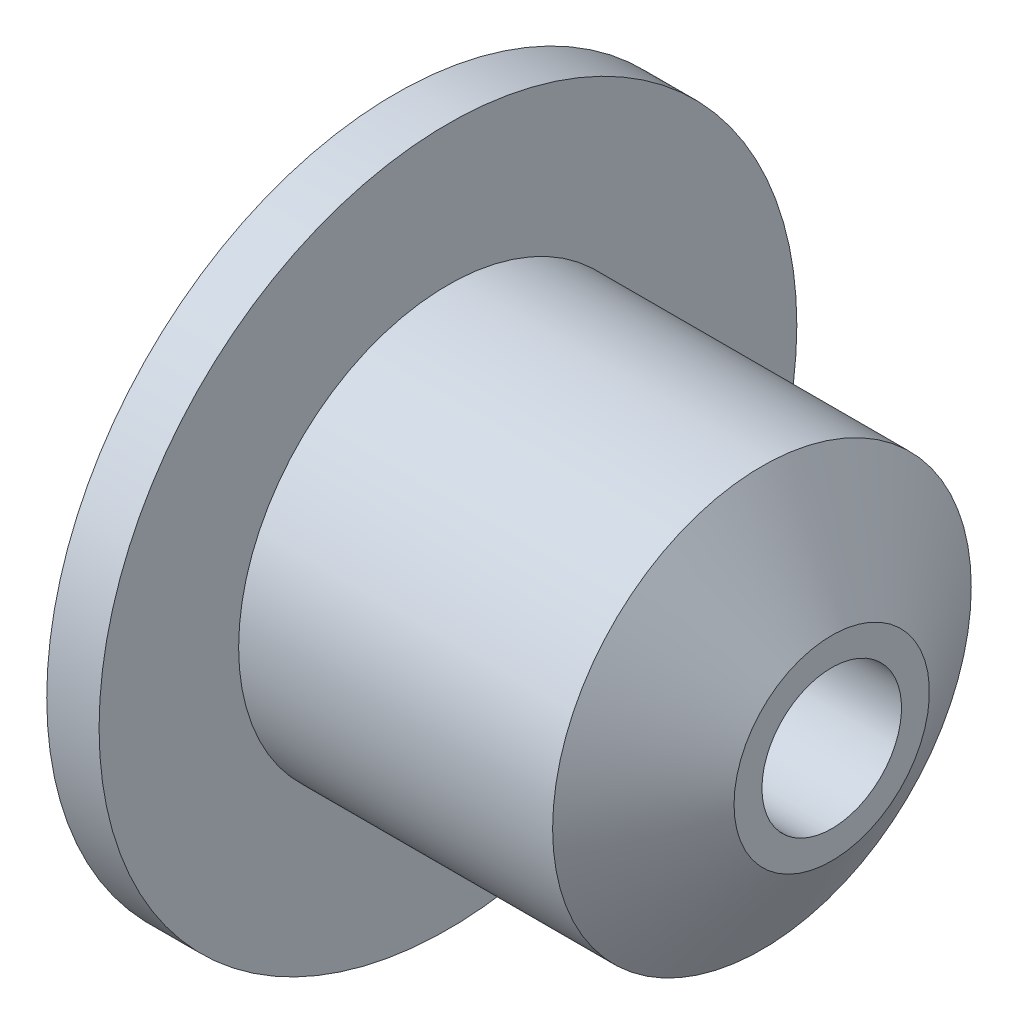
SolidWorks part; units mm, degrees
material "不锈钢 (铁素体)"
ref_plane "前视基准面" through (0, 0, 0) normal (0, 0, 1) x (1, 0, 0)
ref_plane "上视基准面" through (0, 0, 0) normal (0, 1, 0) x (1, 0, 0)
ref_plane "右视基准面" through (0, 0, 0) normal (1, 0, 0) x (0, 0, -1)
sketch "草图1" plane through (0, 0, 0) normal (0, 0, 1) x (1, 0, 0)
  line L0 (-41.1361, 0) -> (40.3287, 0) construction
  line L1 (-34.9258, 2) -> (-34.9258, 10)
  line L2 (-34.9258, 10) -> (-33.4258, 10)
  line L3 (-33.4258, 10) -> (-33.4258, 6)
  line L4 (-33.4258, 6) -> (-24.4258, 6)
  line L6 (-24.4258, 2) -> (-34.9258, 2)
  line L7 (-22.4258, 2) -> (-22.4258, 2.8)
  line L8 (-22.4258, 2) -> (-24.4258, 2)
  line L9 (-22.4258, 2.8) -> (-24.4258, 6)
  dimension "D1" = 4
  dimension "D2" = 12
  dimension "D3" = 9
  dimension "D4" = 1.5
  dimension "D5" = 8
  dimension "D6" = 2
  dimension "D7" = 5.6
revolve "旋转1" add sketch "草图1" angle 360 about L0
